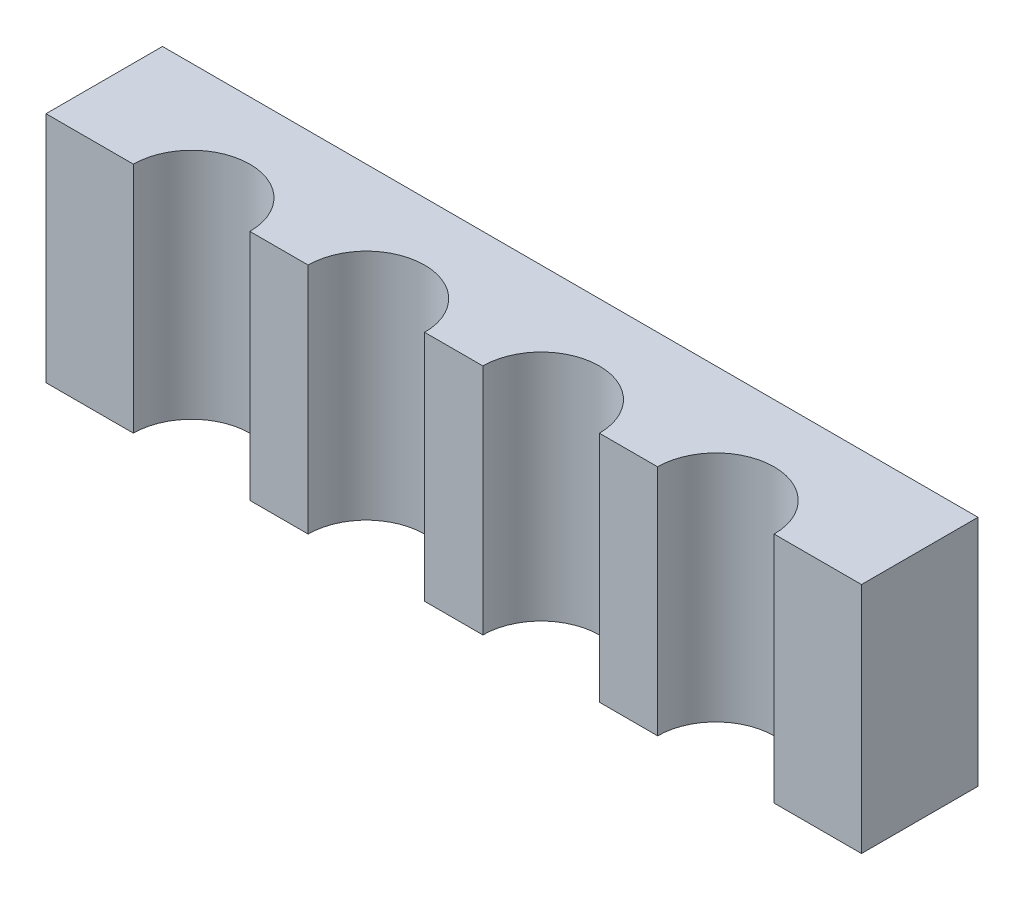
SolidWorks part; units mm, degrees
ref_plane "Front Plane" through (0, 0, 0) normal (0, 0, 1) x (1, 0, 0)
ref_plane "Top Plane" through (0, 0, 0) normal (0, 1, 0) x (1, 0, 0)
ref_plane "Right Plane" through (0, 0, 0) normal (1, 0, 0) x (0, 0, -1)
sketch "Sketch1" plane through (0, 0, 0) normal (0, 1, 0) x (1, 0, 0)
  line L0 (-105, -30) -> (-75, -30)
  line L1 (-210, 30) -> (210, 30)
  line L2 (-210, 30) -> (-210, -30)
  line L3 (-210, -30) -> (-165, -30)
  line L4 (210, 30) -> (210, -30)
  line L5 (-210, 30) -> (210, -30) construction
  line L6 (-210, -30) -> (210, 30) construction
  line L7 (-15, -30) -> (15, -30)
  line L8 (75, -30) -> (105, -30)
  line L9 (165, -30) -> (210, -30)
  arc A0 (-105, -30) -> (-165, -30) centre (-135, -30) ccw
  arc A1 (-15, -30) -> (-75, -30) centre (-45, -30) ccw
  arc A2 (75, -30) -> (15, -30) centre (45, -30) ccw
  arc A3 (165, -30) -> (105, -30) centre (135, -30) ccw
  point P0 (0, 0)
  point P14 (0, 0)
  point P15 (0, 0)
  point P16 (0, 0)
  point P17 (0, 0)
  dimension "D3" = 60
  dimension "D4" = 60
  dimension "D5" = 60
  dimension "D6" = 60
  dimension "D1" = 420
  dimension "D2" = 60
  dimension "D7" = 90
  dimension "D8" = 90
  dimension "D9" = 90
  dimension "D10" = 45
extrude "Boss-Extrude1" add sketch "Sketch1" along normal blind 120
